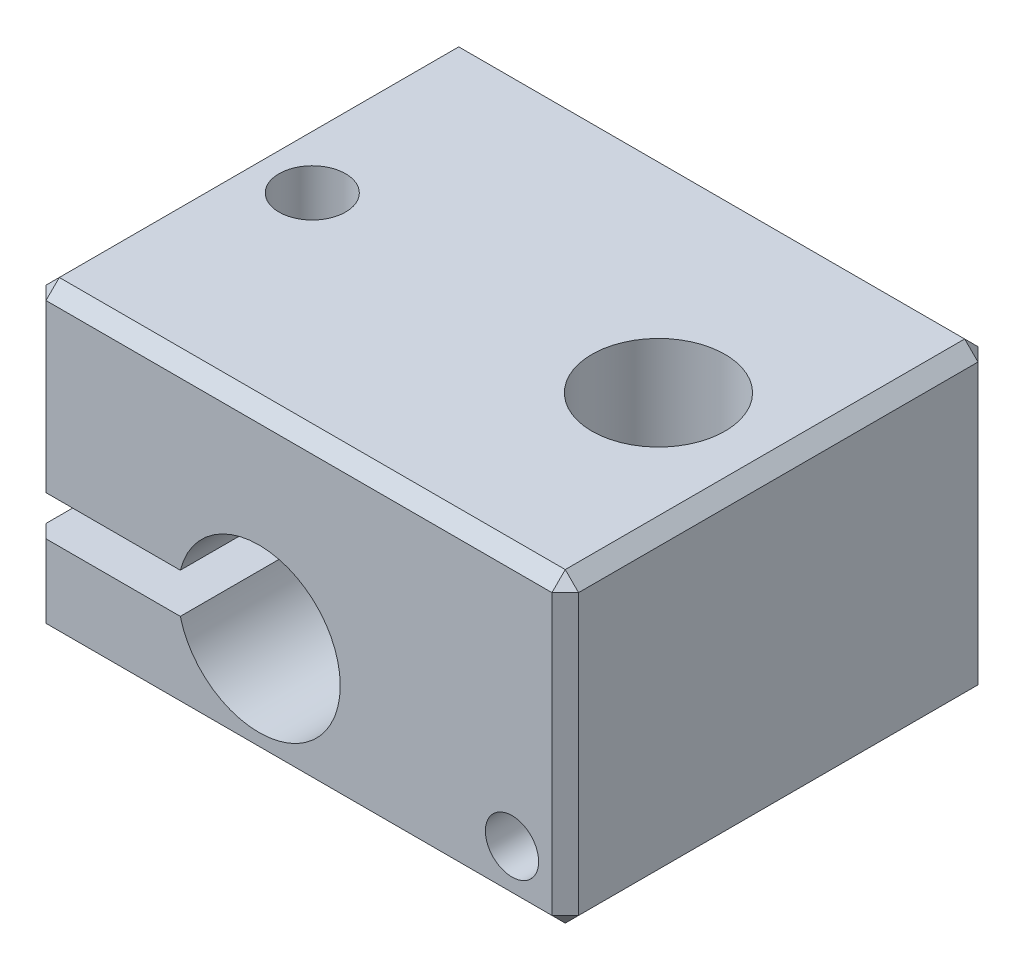
SolidWorks part; units mm, degrees
material "6061 Alloy"
ref_plane "Front Plane" through (0, 0, 0) normal (0, 0, 1) x (1, 0, 0)
ref_plane "Top Plane" through (0, 0, 0) normal (0, 1, 0) x (1, 0, 0)
ref_plane "Right Plane" through (0, 0, 0) normal (1, 0, 0) x (0, 0, -1)
sketch "Sketch1" plane through (0, 0, 0) normal (0, 1, 0) x (1, 0, 0)
  line L1 (0, 0) -> (20, 0)
  line L2 (0, 0) -> (0, 16)
  line L3 (0, 16) -> (20, 16)
  line L4 (20, 0) -> (20, 16)
  dimension "D1" = 16
  dimension "D2" = 20
extrude "Boss-Extrude1" add sketch "Sketch1" along normal blind 11.5
hole_wizard "M3x0.5 Tapped Hole1" positions "Sketch7" profile "Sketch6" tap size "M3x0.5" standard "ANSI Metric" end condition through all
sketch "Sketch7" plane through (0, 11.5, 0) normal (0, 1, 0) x (1, 0, 0)
  line L0 (0, 0) -> (20, 0) construction
  line L1 (20, 0) -> (20, 16) construction
  point P0 (2.5, 8)
  dimension "D1" = 8
  dimension "D2" = 17.5
cosmetic thread "Hole Thread2" parameters "D2"=3
sketch "Sketch6" plane through (2.5, 11.5, -8) normal (1, 0, 0) x (0, 0, 1)
  line L0 (0, 0) -> (0, 11.5)
  line L1 (0, 11.5) -> (1.25, 11.5)
  line L2 (1.25, 11.5) -> (1.25, 0)
  line L5 (1.25, 0) -> (0, 0)
  line L11 (0, -6.35) -> (0, 107.95) construction
  dimension "Thru Tap Drill Dia." = 2.5
  dimension "Thru Tap Drill Depth" = 11.5
hole_wizard "M6 Tapped Hole1" positions "Sketch5" profile "Sketch4" tap size "M6" standard "ISO" end condition through all
sketch "Sketch5" plane through (0, 11.5, 0) normal (0, 1, 0) x (1, 0, 0)
  line L0 (20, 0) -> (20, 16) construction
  line L1 (0, 0) -> (20, 0) construction
  point P0 (15.5, 8)
  dimension "D1" = 4.5
  dimension "D2" = 8
cosmetic thread "Hole Thread1" parameters "D2"=6
sketch "Sketch4" plane through (15.5, 11.5, -8) normal (1, 0, 0) x (0, 0, 1)
  line L0 (0, 0) -> (0, 11.5)
  line L1 (0, 11.5) -> (2.5, 11.5)
  line L2 (2.5, 11.5) -> (2.5, 0)
  line L5 (2.5, 0) -> (0, 0)
  line L11 (0, -6.35) -> (0, 107.95) construction
  dimension "Thru Tap Drill Dia." = 5
  dimension "Thru Tap Drill Depth" = 11.5
sketch "Sketch2" plane through (0, 0, 0) normal (0, 0, 1) x (1, 0, 0)
  line L0 (0, 0) -> (20, 0) construction
  line L1 (20, 11.5) -> (20, 0) construction
  line L2 (0, 11.5) -> (0, 0) construction
  line L3 (0, 4.75) -> (5.5437, 4.75)
  line L4 (0, 4.75) -> (0, 3.25)
  line L5 (0, 3.25) -> (5.5437, 3.25)
  line L6 (5.5437, 4.75) -> (5.5437, 3.25)
  line L7 (2.7718, 3.25) -> (2.7718, 4.75) construction
  line L8 (0, 4) -> (5.5437, 4) construction
  circle A0 centre (8.5, 4) radius 3.05
  point P86 (2.7718, 4)
  line M4 (0, 11.5) -> (0, 0)
  dimension "D2" = 11.5
  dimension "D3" = 6.1
  dimension "D1" = 4
  dimension "D4" = 1.5
extrude "Cut-Extrude1" cut sketch "Sketch2" against normal blind 16 contours A0 L3 L5 M4 | L6 A0 | L6 A0
hole_wizard "M3x0.5 Tapped Hole2" [suppressed] positions "Sketch9" profile "Sketch8" tap size "M3x0.5" standard "ANSI Metric"
sketch "Sketch9" plane through (0, 0, 0) normal (0, 0, 1) x (1, 0, 0)
  line L0 (0, 0) -> (20, 0) construction
  line L1 (20, 11.5) -> (20, 0) construction
  point P0 (16.5, 4.8)
  dimension "D1" = 4.8
  dimension "D2" = 3.5
sketch "Sketch8" plane through (16.5, 4.8, 0) normal (1, 0, 0) x (0, -1, 0)
  line L0 (0, 0) -> (0, 4.1511)
  line L1 (0, 4.1511) -> (1.25, 3.4)
  line L2 (1.25, 3.4) -> (1.25, 0)
  line L5 (1.25, 0) -> (0, 0)
  line L10 (0, 4.1511) -> (-1.25, 3.4) construction
  line L11 (0, -6.35) -> (0, 107.95) construction
  dimension "Tap Drill Dia." = 2.5
  dimension "Tap Drill Depth" = 3.4
  dimension "Drill Angle" = 118
cosmetic thread "Hole Thread3" [suppressed] parameters "D1"=3.4, "D2"=3
sketch "Sketch10" plane through (0, 0, 0) normal (0, 0, 1) x (1, 0, 0)
  line L0 (0, 0) -> (20, 0) construction
  line L1 (20, 11.5) -> (20, 0) construction
  circle A0 centre (18, 2) radius 1
  dimension "D1" = 2
  dimension "D2" = 2
  dimension "D3" = 2
extrude "Cut-Extrude2" cut sketch "Sketch10" against normal blind 2
sketch "Sketch11" plane through (0, 0, -2) normal (0, 0, 1) x (1, 0, 0)
  circle A0 centre (18, 2) radius 0.75
  dimension "D1" = 1.5
extrude "Cut-Extrude3" cut sketch "Sketch11" against normal blind 2.5
chamfer "Chamfer1" distance 0.5 angle 45 14 edges at (0, 1.625, -16) (0, 8.125, -16) (0, 0, -8) (20, 11.5, -8) (10, 0, -16) (20, 5.75, -16) (20, 0, -8) (0, 1.625, 0) (10, 0, 0) (20, 5.75, 0) (0, 8.125, 0) (10, 11.5, 0) (0, 11.5, -8) (10, 11.5, -16)
